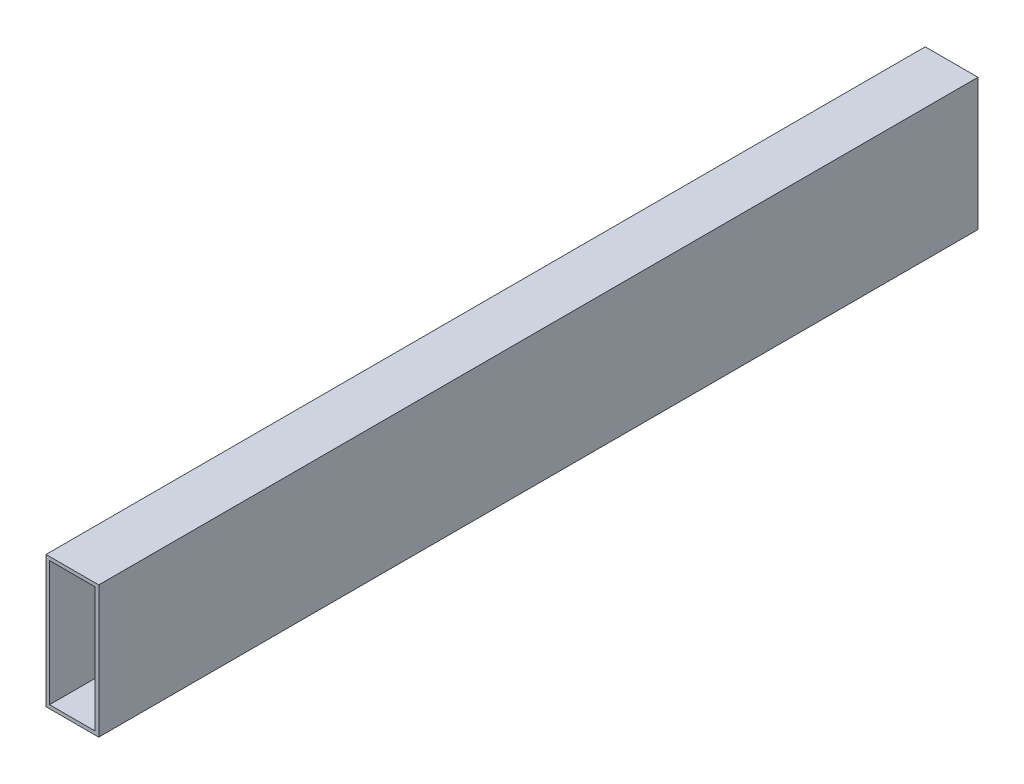
SolidWorks part; units mm, degrees
ref_plane "Front Plane" through (0, 0, 0) normal (0, 0, 1) x (1, 0, 0)
ref_plane "Top Plane" through (0, 0, 0) normal (0, 1, 0) x (1, 0, 0)
ref_plane "Right Plane" through (0, 0, 0) normal (1, 0, 0) x (0, 0, -1)
curve "Curve1"
  spline degree 1 poles (0, 0, -500) (0, 0, 500) knots 0 0 1 1
sketch "Sketch1" plane through (0, 0, 0) normal (0, 0, 1) x (1, 0, 0)
  line L0 (0, 35.3535) -> (0, -33.8384) construction
  line L1 (-30, 75) -> (30, 75)
  line L2 (-30, 75) -> (-30, -75)
  line L3 (-30, -75) -> (30, -75)
  line L4 (30, 75) -> (30, -75)
  line L5 (-26, 71) -> (26, 71)
  line L6 (-26, 71) -> (-26, -71)
  line L7 (-26, -71) -> (26, -71)
  line L8 (26, 71) -> (26, -71)
  line L9 (-39.3939, 0) -> (41.5152, 0) construction
  dimension "D1" = 60
  dimension "D2" = 52
  dimension "D3" = 150
  dimension "D4" = 142
sweep "Sweep1" add profiles "Sketch1" path "Curve1"
